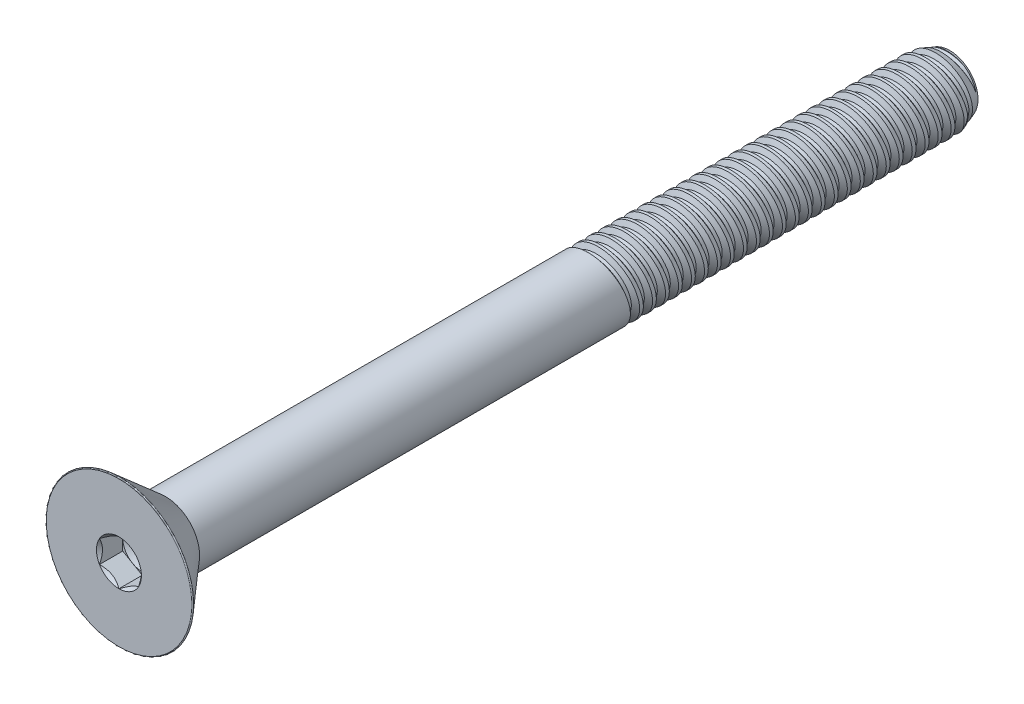
SolidWorks part; units mm, degrees
ref_plane "Front" through (0, 0, 0) normal (0, 0, 1) x (1, 0, 0)
ref_plane "Top" through (0, 0, 0) normal (0, 1, 0) x (1, 0, 0)
ref_plane "Right" through (0, 0, 0) normal (1, 0, 0) x (0, 0, -1)
sketch "Sketch1" plane through (0, 0, 0) normal (1, 0, 0) x (0, 0, -1)
  line L0 (0, 0) -> (-2.8448, 0) construction
  line L1 (0, 0) -> (47.9552, 0)
  line L2 (0, 0) -> (0, 2.0828)
  line L3 (0, 2.0828) -> (47.9552, 2.0828)
  line L4 (47.9552, 0) -> (47.9552, 2.0828)
  line L5 (0, -2.0828) -> (47.9552, -2.0828) construction
  dimension "Thread Dia" = 4.1656
  dimension "Length" = 50.8
  dimension "Head Height" = 2.8448
revolve "Revolve1" add sketch "Sketch1" angle 360 about L0
ref_plane "Plane1" through (0, 0, 2.8448) normal (0, 0, 1) x (1, 0, 0)
sketch "Sketch2" plane through (0, 0, 0) normal (1, 0, 0) x (0, 0, -1)
  line L0 (25.7302, 2.0828) -> (25.7302, -2.0828) construction
  line L1 (25.7302, -2.0828) -> (26.5239, -2.0828) construction
  line L2 (26.5239, -2.0828) -> (25.7302, 2.0828) construction
  line L3 (25.7302, 2.0828) -> (25.8277, 2.1014) construction
  line L4 (25.8277, 2.1014) -> (26.5099, 2.2314)
  line L5 (26.5099, 2.2314) -> (26.3467, 1.7629)
  line L6 (26.3467, 1.7629) -> (26.1517, 1.7258)
  line L7 (26.1517, 1.7258) -> (25.8277, 2.1014)
  line L8 (26.2492, 1.7443) -> (26.1688, 2.1664) construction
  line L9 (0, -2.0828) -> (47.9552, -2.0828) construction
  line L10 (0, 2.0828) -> (47.9552, 2.0828) construction
  line L11 (47.9552, 0) -> (47.9552, 2.0828) construction
  line L12 (26.1847, 2.0828) -> (26.9785, -2.0828) construction
  line L13 (25.7302, -0.1622) -> (27.433, 0.1622) construction
  line L14 (-250.4948, 2.0828) -> (-250.4948, -2.0828) construction
  point P19 (26.5816, 0)
  dimension "D1" = 60
  dimension "Thread Pitch" = 0.7937
  dimension "D2" = 0.0992
  dimension "D3" = 0.1984
  dimension "D4" = 0.7937
  dimension "Thread Length" = 298.45
  dimension "Min Thread Length" = 22.225
revolve "Cut-Revolve1" cut sketch "Sketch2" angle 360 about L13
sketch "Sketch3" plane through (0, 0, 0) normal (1, 0, 0) x (0, 0, -1)
  line L0 (47.9552, 1.7258) -> (46.9743, 2.0828)
  line L1 (46.9743, 2.0828) -> (47.9552, 2.0828)
  line L2 (47.9552, 2.0828) -> (47.9552, 1.7258)
  line L3 (0, 2.0828) -> (47.9552, 2.0828) construction
  line L4 (47.9552, 0) -> (47.9552, 2.0828) construction
  line L5 (46.9743, 0) -> (0, 0) construction
  line L6 (46.9743, 2.0828) -> (46.9743, -2.0828) construction
  line L7 (0, -2.0828) -> (47.9552, -2.0828) construction
  dimension "D1" = 20
  dimension "D2" = 4.1656
revolve "Cut-Revolve2" cut sketch "Sketch3" angle 360 about L5
pattern_linear "LPattern1" count 28 spacing 0.7937 along (0, 0, -1) of "Cut-Revolve1"
sketch "Sketch4" plane through (0, 0, 0) normal (0, 0, 1) x (1, 0, 0)
  circle A0 centre (0, 0) radius 4.5593
  dimension "Head Dia" = 9.1186
extrude "Extrude1" add sketch "Sketch4" along normal up to surface (2.8448 mm away) up to plane "Plane1"
sketch "Sketch9" plane through (0, 0, 0) normal (1, 0, 0) x (0, 0, -1)
  line L0 (-2.8448, 4.5593) -> (0, 2.0864)
  line L1 (0, 2.0864) -> (0, 4.5593)
  line L2 (0, 4.5593) -> (-2.8448, 4.5593)
  line L3 (0, 0) -> (-2.8448, 0) construction
  line L6 (-2.8448, -4.5593) -> (0, -2.0864) construction
  line L7 (0, -4.5593) -> (0, 4.5593) construction
  line L8 (-2.8448, 4.5593) -> (-2.8448, -4.5593) construction
  line L9 (0, 4.5593) -> (-2.8448, 4.5593) construction
  dimension "D1" = 82
revolve "Cut-Revolve3" cut sketch "Sketch9" angle 360 about L3
fillet "Fillet1" radius 0.0508 1 edges at (0, 4.5593, 2.8448)
sketch "Sketch6" plane through (0, 0, 2.8448) normal (0, 0, 1) x (1, 0, 0)
  line L1 (0, -1.3748) -> (1.1906, -0.6874)
  line L2 (1.1906, -0.6874) -> (1.1906, 0.6874)
  line L3 (1.1906, 0.6874) -> (0, 1.3748)
  line L4 (0, 1.3748) -> (-1.1906, 0.6874)
  line L5 (-1.1906, 0.6874) -> (-1.1906, -0.6874)
  line L6 (-1.1906, -0.6874) -> (0, -1.3748)
  circle A0 centre (0, 0) radius 1.1906 construction
  dimension "Hex" = 2.3813
extrude "Cut-Extrude1" cut sketch "Sketch6" against normal blind 1.4224
sketch "Sketch7" plane through (0, 0, 2.8448) normal (0, 0, 1) x (1, 0, 0)
  circle A0 centre (0, 0) radius 1.3748
extrude "Cut-Extrude4" cut sketch "Sketch7" against normal blind 1.4224 draft 45
sketch "Sketch8" plane through (0, 0, 1.4224) normal (0, 0, 1) x (1, 0, 0)
  circle A0 centre (0, 0) radius 1.1906 construction
  circle A1 centre (0, 0) radius 1.1906
extrude "Cut-Extrude5" cut sketch "Sketch8" against normal blind 0.4741 draft 60
equation "\"D2@Sketch2\"=\"Thread Pitch@Sketch2\"/8"
equation "\"D3@Sketch2\"=\"Thread Pitch@Sketch2\"/4"
equation "\"D4@Sketch2\"=\"Thread Pitch@Sketch2\""
equation "\"D3@LPattern1\"=\"Thread Pitch@Sketch2\""
equation "\"D1@LPattern1\"=\"Min Thread Length@Sketch2\"/\"Thread Pitch@Sketch2\""
equation "\"D1@Cut-Extrude1\"=\"Head Height@Sketch1\"/2"
equation "\"D1@Cut-Extrude4\"=\"D1@Cut-Extrude1\""
equation "\"D1@Cut-Extrude5\"=\"D1@Cut-Extrude1\"/3"
